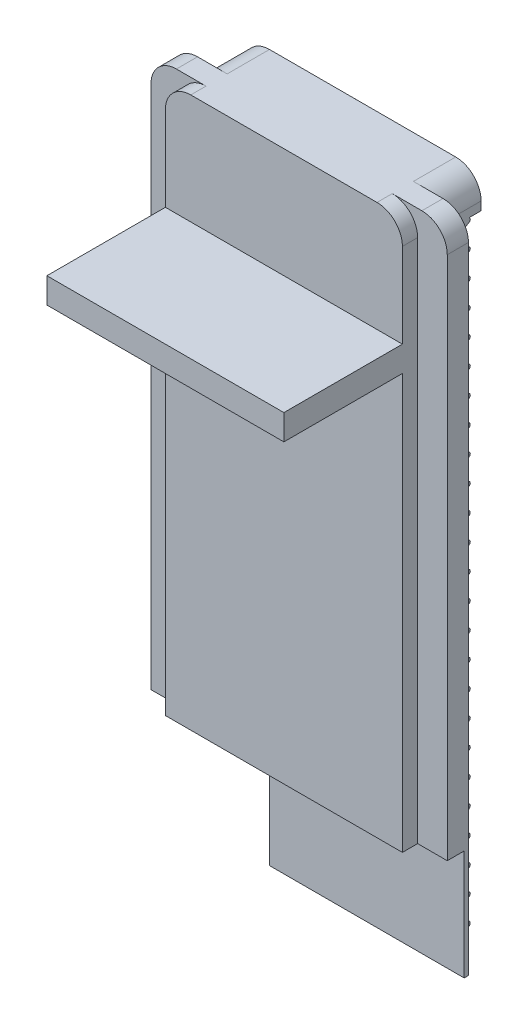
SolidWorks part; units mm, degrees
ref_plane "Plano frontal" through (0, 0, 0) normal (0, 0, 1) x (1, 0, 0)
ref_plane "Plano superior" through (0, 0, 0) normal (0, 1, 0) x (1, 0, 0)
ref_plane "Plano direito" through (0, 0, 0) normal (1, 0, 0) x (0, 0, -1)
sketch "Esboço1" plane through (0, 0, 0) normal (0, 0, 1) x (1, 0, 0)
  line L0 (0, 0) -> (0, 129.2301) construction
  line L1 (-14, 0) -> (14, 0)
  line L2 (14, 0) -> (14, 78)
  line L3 (14, 78) -> (-14, 78)
  line L8 (-14, 0) -> (-14, 78)
  point P12 (0, 136)
  dimension "D1" = 28
  dimension "D2" = 78
extrude "Ressalto-extrusão1" add sketch "Esboço1" along normal blind 3.2
sketch "Esboço3" plane through (-14, 0, 0) normal (-1, 0, 0) x (0, 0, 1)
  line L0 (-0.1457, 0.3572) -> (-2.0713, 1.5126)
  line L1 (-2.0713, 2.0271) -> (-0.1457, 3.1825)
  line L2 (0, 78) -> (0, 0) construction
  line L4 (0, 3.4397) -> (0, 3.5397)
  line L5 (0, 78) -> (0, 0) construction
  line L6 (0, 3.5397) -> (0.2, 3.5397)
  line L7 (0.2, 3.5397) -> (0.2, 0)
  line L8 (0.2, 0) -> (0, 0)
  line L9 (0, 0) -> (0, 0.1)
  arc A0 (-0.1457, 3.1825) -> (0, 3.4397) centre (-0.3, 3.4397) ccw
  arc A1 (-2.0713, 1.5126) -> (-2.0713, 2.0271) centre (-1.9169, 1.7699) cw
  arc A2 (-0.1457, 0.3572) -> (0, 0.1) centre (-0.3, 0.1) cw
  point P17 (0, 3.2699)
  point P18 (0.2, 1.7699)
  point P21 (-2.5, 1.7699)
  point P24 (0, 0.2699)
  dimension "D3" = 0.3
  dimension "D1" = 2.5
  dimension "D2" = 3
  dimension "D4" = 0.1
  dimension "D5" = 0.2
extrude "Ressalto-extrusão3" add sketch "Esboço3" against normal up to surface (28 mm away) up to face at (14, 39, 1.6)
pattern_linear "Padrão linear1" count 25 spacing 3 along (0, 1, 0) of "Ressalto-extrusão3"
sketch "Esboço6" plane through (0, 78, 0) normal (0, 1, 0) x (1, 0, 0)
  line L0 (-14, 0) -> (-14, -1.5)
  line L1 (-14, -1.5) -> (-17.5, -1.5)
  line L2 (-17.5, -1.5) -> (-17.5, -4)
  line L3 (-17.5, -4) -> (-14, -4)
  line L4 (-14, -4) -> (-14, -7)
  line L5 (-14, -7) -> (14, -7)
  line L6 (0, -7) -> (0, 0) construction
  line L8 (-14, 0) -> (0, 0)
  line L9 (14, 0) -> (0, 0)
  line L10 (14, -4) -> (14, -7)
  line L11 (17.5, -4) -> (14, -4)
  line L12 (17.5, -1.5) -> (17.5, -4)
  line L13 (14, -1.5) -> (17.5, -1.5)
  line L14 (14, 0) -> (14, -1.5)
  line L15 (-14, 0) -> (14, 0)
  line M8 (-14, -3.2) -> (14, -3.2)
  dimension "D1" = 2.5
  dimension "D2" = 3
  dimension "D3" = 3.5
  dimension "D4" = 7
extrude "Ressalto-extrusão4" add sketch "Esboço6" against normal up to surface (78 mm away) contours L6 L5 L10 L11 L12 L13 L14 M8 | L5 L6 L0 L1 L2 L3 L4 M8 up to face at (0, 0, 1.6)
sketch "Esboço7" plane through (0, 0, 7) normal (0, 0, 1) x (1, 0, 0)
  line L0 (14, 0) -> (14, 78) construction
  line L1 (-14, 5) -> (14, 5)
  line L2 (-14, 5) -> (-14, 78)
  line L3 (-14, 78) -> (14, 78)
  line L4 (14, 5) -> (14, 78)
  line L5 (-14, 0) -> (-14, 78) construction
  line L6 (14, 0) -> (-14, 0) construction
  dimension "D1" = 5
extrude "Corte-extrusão1" cut sketch "Esboço7" against normal blind 1.2
sketch "Esboço8" plane through (0, 0, 0) normal (0, 0, -1) x (-1, 0, 0)
  line L0 (14, 78) -> (14, 75.4397) construction
  line L1 (-14, 78) -> (14, 78)
  line L2 (-14, 78) -> (-14, 74)
  line L3 (-14, 74) -> (14, 74)
  line L4 (14, 78) -> (14, 74)
  dimension "D1" = 4
extrude "Ressalto-extrusão5" add sketch "Esboço8" along normal blind 3.5
fillet "Filete1" radius 3 6 edges at (14, 78, 4.9) (17.5, 78, 2.75) (14, 78, -1) (-14, 78, 4.9) (-17.5, 78, 2.75) (-14, 78, -1)
sketch "Esboço9" plane through (0, 0, 0) normal (0, -1, 0) x (1, 0, 0)
  line L0 (17.5, 2) -> (-5.5, 2)
  line L1 (-5.5, -3.5) -> (-17.5, -3.5)
  line L2 (17.5, 2) -> (17.5, 8.2945)
  line L3 (17.5, 8.2945) -> (-17.5, 8.2945)
  line L4 (-17.5, -3.5) -> (-17.5, 8.2945)
  line L5 (-5.5, 2) -> (-5.5, -3.5)
  line L6 (14, -3.5) -> (-14, -3.5) construction
  line L7 (17.5, 4) -> (17.5, 1.5) construction
  line L8 (14, 7) -> (-14, 7) construction
  point P0 (-6.2619, -3.5)
  dimension "D1" = 5
  dimension "D2" = 12
extrude "Corte-extrusão2" cut sketch "Esboço9" against normal blind 13
sketch "Esboço11" plane through (-14, 0, 0) normal (-1, 0, 0) x (0, 0, 1)
  line L0 (4, 65) -> (19.8, 65)
  line L1 (4, 13) -> (4, 75) construction
  line L2 (19.8, 65) -> (19.8, 62)
  line L3 (19.8, 62) -> (4, 62)
  line L4 (4, 13) -> (4, 75) construction
  line L5 (4, 62) -> (4, 65)
  line L6 (4, 78) -> (5.8, 78) construction
  line L7 (5.8, 75) -> (5.8, 13) construction
  point P12 (19.8, 63.5)
  dimension "D1" = 14
  dimension "D2" = 3
  dimension "D3" = 13
extrude "Ressalto-extrusão6" add sketch "Esboço11" against normal up to surface (28 mm away) up to face at (14, 44, 4.9)
